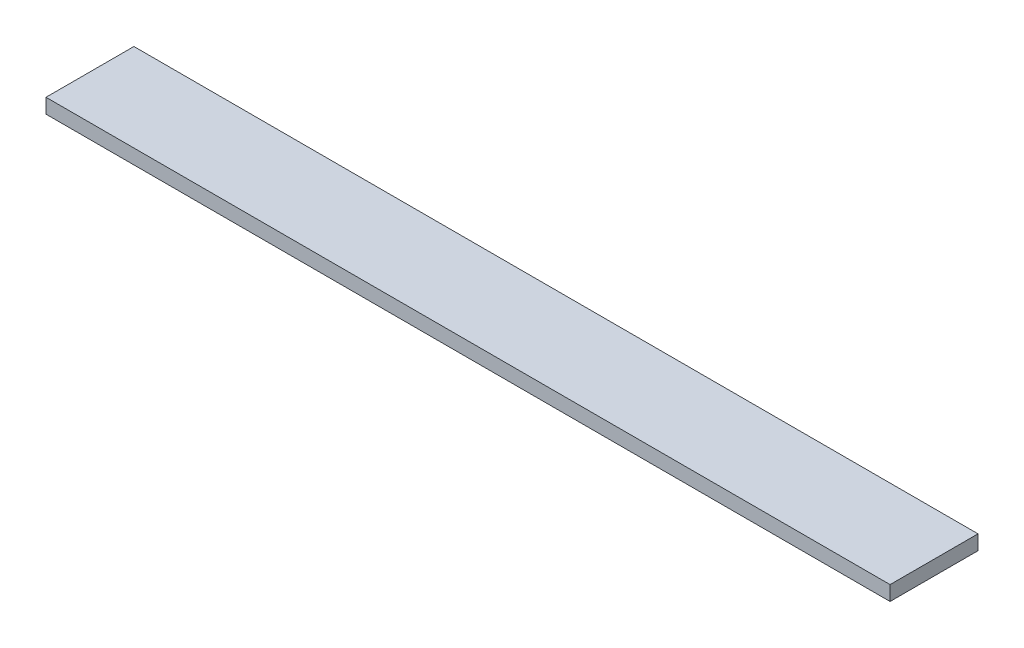
SolidWorks part; units mm, degrees
ref_plane "Front Plane" through (0, 0, 0) normal (0, 0, 1) x (1, 0, 0)
ref_plane "Top Plane" through (0, 0, 0) normal (0, 1, 0) x (1, 0, 0)
ref_plane "Right Plane" through (0, 0, 0) normal (1, 0, 0) x (0, 0, -1)
sketch "Sketch1" plane through (0, 0, 0) normal (0, 1, 0) x (1, 0, 0)
  line L1 (0, 0) -> (914.4, 0)
  line L2 (0, 0) -> (0, 95.25)
  line L3 (0, 95.25) -> (914.4, 95.25)
  line L4 (914.4, 0) -> (914.4, 95.25)
  dimension "D1" = 95.25
  dimension "D2" = 914.4
extrude "Boss-Extrude1" add sketch "Sketch1" along normal blind 15.875
